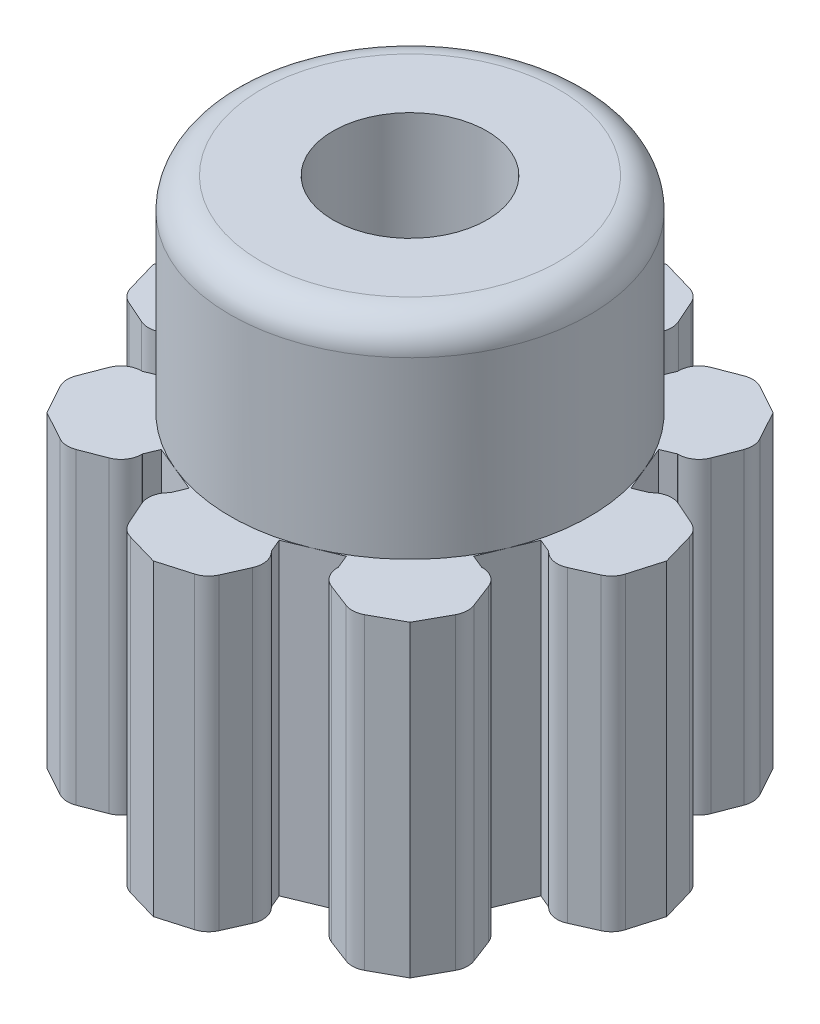
SolidWorks part; units mm, degrees
material "Polyethylene Cross-Linked"
ref_plane "Front Plane" through (0, 0, 0) normal (0, 0, 1) x (1, 0, 0)
ref_plane "Top Plane" through (0, 0, 0) normal (0, 1, 0) x (1, 0, 0)
ref_plane "Right Plane" through (0, 0, 0) normal (1, 0, 0) x (0, 0, -1)
sketch "Sketch1" plane through (0, 0, 0) normal (0, 1, 0) x (1, 0, 0)
  circle A0 centre (0, 0) radius 2.5
  dimension "D1" = 5
extrude "Boss-Extrude1" add sketch "Sketch1" along normal blind 3
sketch "Sketch2" plane through (0, 3, 0) normal (0, 1, 0) x (1, 0, 0)
  circle A0 centre (0, 0) radius 1.75
  dimension "D1" = 3.5
extrude "Boss-Extrude2" add sketch "Sketch2" along normal blind 2
sketch "Sketch3" plane through (0, 5, 0) normal (0, 1, 0) x (1, 0, 0)
  circle A0 centre (0, 0) radius 0.75
  circle A1 centre (0, 0) radius 1.75 construction
  dimension "D1" = 1
extrude "Cut-Extrude1" cut sketch "Sketch3" against normal through all
sketch "Sketch4" plane through (0, 3, 0) normal (0, 1, 0) x (1, 0, 0)
  line L0 (0, 0) -> (-2.5, 0) construction
  line L1 (0, 0) -> (-1.7678, 1.7678) construction
  line L2 (0, 0) -> (0, 2.5) construction
  line L3 (0, 0) -> (1.7678, 1.7678) construction
  line L4 (0, 0) -> (2.5, 0) construction
  line L5 (0, 0) -> (1.7678, -1.7678) construction
  line L6 (0, 0) -> (0, -2.5) construction
  line L7 (0, 0) -> (-1.7678, -1.7678) construction
  line L8 (-2.5, 0) -> (-1.7678, 1.7678) construction
  line L9 (-2.3097, 0.9567) -> (-1.6168, 0.6697) construction
  line L10 (-1.7125, 0.4387) -> (-1.5211, 0.9007)
  line L11 (-1.7125, 0.4387) -> (-1.843, 0.4928)
  line L12 (-1.843, 0.4928) -> (-1.8492, 0.499)
  line L13 (-2.072, 0.5403) -> (-2.2988, 0.4393)
  line L14 (-2.4095, 0.3123) -> (-2.5, 0)
  line L15 (-1.5211, 0.9007) -> (-1.6516, 0.9547)
  line L16 (-1.8472, 1.0831) -> (-1.9361, 1.3149)
  line L17 (-1.9246, 1.483) -> (-1.7678, 1.7678)
  line L18 (-1.6516, 0.9547) -> (-1.6605, 0.9547)
  line L19 (-1.483, 1.9246) -> (-1.7678, 1.7678)
  line L20 (-1.0831, 1.8472) -> (-1.3149, 1.9361)
  line L21 (-0.9007, 1.5211) -> (-0.9547, 1.6516)
  line L22 (-0.9547, 1.6516) -> (-0.9547, 1.6605)
  line L23 (-0.9007, 1.5211) -> (-0.4387, 1.7125)
  line L24 (-0.4387, 1.7125) -> (-0.4928, 1.843)
  line L25 (-0.4928, 1.843) -> (-0.499, 1.8492)
  line L26 (-0.5403, 2.072) -> (-0.4393, 2.2988)
  line L27 (-0.3123, 2.4095) -> (0, 2.5)
  line L28 (0.3123, 2.4095) -> (0, 2.5)
  line L29 (0.5403, 2.072) -> (0.4393, 2.2988)
  line L30 (0.4387, 1.7125) -> (0.4928, 1.843)
  line L31 (0.4928, 1.843) -> (0.499, 1.8492)
  line L32 (0.4387, 1.7125) -> (0.9007, 1.5211)
  line L33 (0.9007, 1.5211) -> (0.9547, 1.6516)
  line L34 (0.9547, 1.6516) -> (0.9547, 1.6605)
  line L35 (1.0831, 1.8472) -> (1.3149, 1.9361)
  line L36 (1.483, 1.9246) -> (1.7678, 1.7678)
  line L37 (1.9246, 1.483) -> (1.7678, 1.7678)
  line L38 (1.8472, 1.0831) -> (1.9361, 1.3149)
  line L39 (1.5211, 0.9007) -> (1.6516, 0.9547)
  line L40 (1.6516, 0.9547) -> (1.6605, 0.9547)
  line L41 (1.5211, 0.9007) -> (1.7125, 0.4387)
  line L42 (1.7125, 0.4387) -> (1.843, 0.4928)
  line L43 (1.843, 0.4928) -> (1.8492, 0.499)
  line L44 (2.072, 0.5403) -> (2.2988, 0.4393)
  line L45 (2.4095, 0.3123) -> (2.5, 0)
  line L46 (2.4095, -0.3123) -> (2.5, 0)
  line L47 (2.072, -0.5403) -> (2.2988, -0.4393)
  line L48 (1.7125, -0.4387) -> (1.843, -0.4928)
  line L49 (1.843, -0.4928) -> (1.8492, -0.499)
  line L50 (1.7125, -0.4387) -> (1.5211, -0.9007)
  line L51 (1.5211, -0.9007) -> (1.6516, -0.9547)
  line L52 (1.6516, -0.9547) -> (1.6605, -0.9547)
  line L53 (1.8472, -1.0831) -> (1.9361, -1.3149)
  line L54 (1.9246, -1.483) -> (1.7678, -1.7678)
  line L55 (1.483, -1.9246) -> (1.7678, -1.7678)
  line L56 (1.0831, -1.8472) -> (1.3149, -1.9361)
  line L57 (0.9007, -1.5211) -> (0.9547, -1.6516)
  line L58 (0.9547, -1.6516) -> (0.9547, -1.6605)
  line L59 (0.9007, -1.5211) -> (0.4387, -1.7125)
  line L60 (0.4387, -1.7125) -> (0.4928, -1.843)
  line L61 (0.4928, -1.843) -> (0.499, -1.8492)
  line L62 (0.5403, -2.072) -> (0.4393, -2.2988)
  line L63 (0.3123, -2.4095) -> (0, -2.5)
  line L64 (-0.3123, -2.4095) -> (0, -2.5)
  line L65 (-0.5403, -2.072) -> (-0.4393, -2.2988)
  line L66 (-0.4387, -1.7125) -> (-0.4928, -1.843)
  line L67 (-0.4928, -1.843) -> (-0.499, -1.8492)
  line L68 (-0.4387, -1.7125) -> (-0.9007, -1.5211)
  line L69 (-0.9007, -1.5211) -> (-0.9547, -1.6516)
  line L70 (-0.9547, -1.6516) -> (-0.9547, -1.6605)
  line L71 (-1.0831, -1.8472) -> (-1.3149, -1.9361)
  line L72 (-1.483, -1.9246) -> (-1.7678, -1.7678)
  line L73 (-1.9246, -1.483) -> (-1.7678, -1.7678)
  line L74 (-1.8472, -1.0831) -> (-1.9361, -1.3149)
  line L75 (-1.5211, -0.9007) -> (-1.6516, -0.9547)
  line L76 (-1.6516, -0.9547) -> (-1.6605, -0.9547)
  line L77 (-1.5211, -0.9007) -> (-1.7125, -0.4387)
  line L78 (-1.7125, -0.4387) -> (-1.843, -0.4928)
  line L79 (-1.843, -0.4928) -> (-1.8492, -0.499)
  line L80 (-2.072, -0.5403) -> (-2.2988, -0.4393)
  line L81 (-2.4095, -0.3123) -> (-2.5, 0)
  circle A0 centre (0, 0) radius 2.5 construction
  circle A1 centre (0, 0) radius 1.75 construction
  arc A2 (-2.2988, 0.4393) -> (-2.4095, 0.3123) centre (-2.2174, 0.2566) ccw
  arc A3 (-1.8492, 0.499) -> (-2.072, 0.5403) centre (-1.9906, 0.3576) ccw
  arc A4 (-1.6605, 0.9547) -> (-1.8472, 1.0831) centre (-1.6605, 1.1547) cw
  arc A5 (-1.9361, 1.3149) -> (-1.9246, 1.483) centre (-1.7494, 1.3865) cw
  arc A6 (-1.3149, 1.9361) -> (-1.483, 1.9246) centre (-1.3865, 1.7494) ccw
  arc A7 (-0.9547, 1.6605) -> (-1.0831, 1.8472) centre (-1.1547, 1.6605) ccw
  arc A8 (-0.499, 1.8492) -> (-0.5403, 2.072) centre (-0.3576, 1.9906) cw
  arc A9 (-0.4393, 2.2988) -> (-0.3123, 2.4095) centre (-0.2566, 2.2174) cw
  arc A10 (0.4393, 2.2988) -> (0.3123, 2.4095) centre (0.2566, 2.2174) ccw
  arc A11 (0.499, 1.8492) -> (0.5403, 2.072) centre (0.3576, 1.9906) ccw
  arc A12 (0.9547, 1.6605) -> (1.0831, 1.8472) centre (1.1547, 1.6605) cw
  arc A13 (1.3149, 1.9361) -> (1.483, 1.9246) centre (1.3865, 1.7494) cw
  arc A14 (1.9361, 1.3149) -> (1.9246, 1.483) centre (1.7494, 1.3865) ccw
  arc A15 (1.6605, 0.9547) -> (1.8472, 1.0831) centre (1.6605, 1.1547) ccw
  arc A16 (1.8492, 0.499) -> (2.072, 0.5403) centre (1.9906, 0.3576) cw
  arc A17 (2.2988, 0.4393) -> (2.4095, 0.3123) centre (2.2174, 0.2566) cw
  arc A18 (2.2988, -0.4393) -> (2.4095, -0.3123) centre (2.2174, -0.2566) ccw
  arc A19 (1.8492, -0.499) -> (2.072, -0.5403) centre (1.9906, -0.3576) ccw
  arc A20 (1.6605, -0.9547) -> (1.8472, -1.0831) centre (1.6605, -1.1547) cw
  arc A21 (1.9361, -1.3149) -> (1.9246, -1.483) centre (1.7494, -1.3865) cw
  arc A22 (1.3149, -1.9361) -> (1.483, -1.9246) centre (1.3865, -1.7494) ccw
  arc A23 (0.9547, -1.6605) -> (1.0831, -1.8472) centre (1.1547, -1.6605) ccw
  arc A24 (0.499, -1.8492) -> (0.5403, -2.072) centre (0.3576, -1.9906) cw
  arc A25 (0.4393, -2.2988) -> (0.3123, -2.4095) centre (0.2566, -2.2174) cw
  arc A26 (-0.4393, -2.2988) -> (-0.3123, -2.4095) centre (-0.2566, -2.2174) ccw
  arc A27 (-0.499, -1.8492) -> (-0.5403, -2.072) centre (-0.3576, -1.9906) ccw
  arc A28 (-0.9547, -1.6605) -> (-1.0831, -1.8472) centre (-1.1547, -1.6605) cw
  arc A29 (-1.3149, -1.9361) -> (-1.483, -1.9246) centre (-1.3865, -1.7494) cw
  arc A30 (-1.9361, -1.3149) -> (-1.9246, -1.483) centre (-1.7494, -1.3865) ccw
  arc A31 (-1.6605, -0.9547) -> (-1.8472, -1.0831) centre (-1.6605, -1.1547) ccw
  arc A32 (-1.8492, -0.499) -> (-2.072, -0.5403) centre (-1.9906, -0.3576) cw
  arc A33 (-2.2988, -0.4393) -> (-2.4095, -0.3123) centre (-2.2174, -0.2566) cw
  circle A34 centre (0, 0) radius 2.7502
  dimension "D3" = 0.2
  dimension "D4" = 0.2
  dimension "D2" = 0.5
  dimension "D1" = 8
  dimension "D5" = 8
extrude "Cut-Extrude3" cut sketch "Sketch4" against normal through all
sketch "Sketch5" plane through (0, 0, 0) normal (0, -1, 0) x (1, 0, 0)
  circle A0 centre (0, 0) radius 1.6284
extrude "Cut-Extrude4" cut sketch "Sketch5" against normal blind 0.1
fillet "Fillet1" radius 0.3 1 edges at (0, 5, 1.75)
